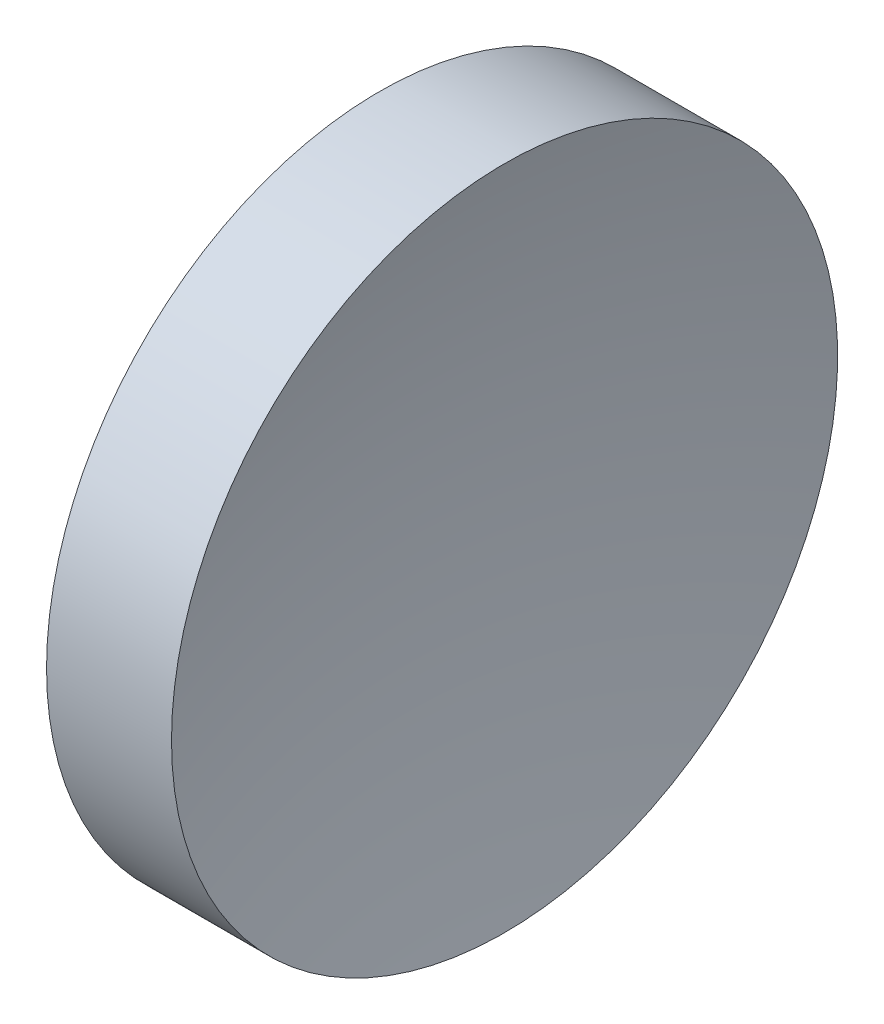
SolidWorks part; units mm, degrees
ref_plane "前视基准面" through (0, 0, 0) normal (0, 0, 1) x (1, 0, 0)
ref_plane "上视基准面" through (0, 0, 0) normal (0, 1, 0) x (1, 0, 0)
ref_plane "右视基准面" through (0, 0, 0) normal (1, 0, 0) x (0, 0, -1)
sketch "草图1" plane through (0, 0, 0) normal (0, 1, 0) x (1, 0, 0)
  line L0 (0, 0) -> (6.9328, 0) construction
  line L1 (0, 0) -> (6.25, 0)
  line L2 (0, 0) -> (0, 25.4)
  line L3 (0, 25.4) -> (9.5296, 25.4)
  arc A0 (9.5296, 25.4) -> (6.25, 0) centre (106.25, 0) ccw
  dimension "D3" = 100
  dimension "D1" = 6.25
  dimension "D2" = 25.4
revolve "旋转1" add sketch "草图1" angle 360 about L0
